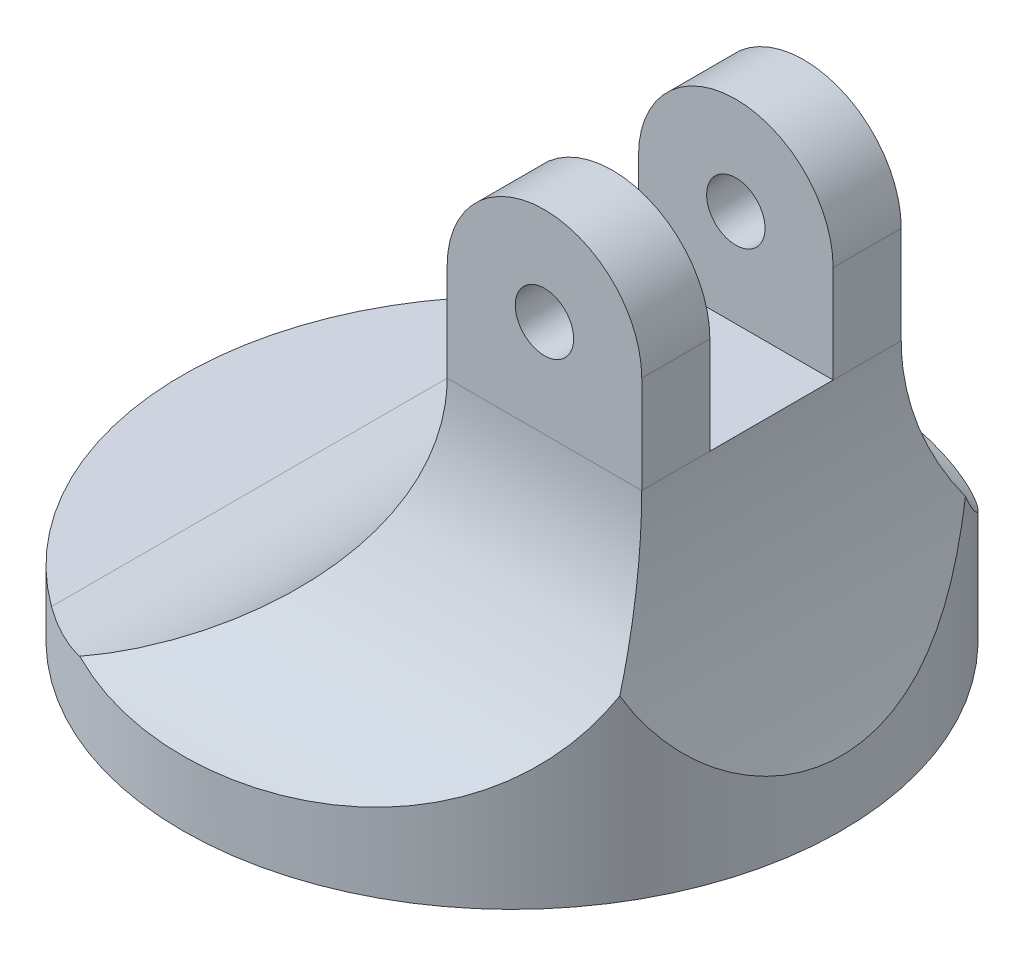
SolidWorks part; units mm, degrees
ref_plane "Front Plane" through (0, 0, 0) normal (0, 0, 1) x (1, 0, 0)
ref_plane "Top Plane" through (0, 0, 0) normal (0, 1, 0) x (1, 0, 0)
ref_plane "Right Plane" through (0, 0, 0) normal (1, 0, 0) x (0, 0, -1)
sketch "Sketch1" plane through (0, 0, 0) normal (0, 1, 0) x (1, 0, 0)
  circle A0 centre (0, 0) radius 25.4
  dimension "D1" = 50.8
extrude "base" add sketch "Sketch1" along normal blind 25
sketch "Sketch3" plane through (0, 0, 0) normal (0, 0, 1) x (1, 0, 0)
  line L0 (5, 25) -> (20, 25)
  line L1 (25.4, 25) -> (-25.4, 25) construction
  line L2 (-25.4, 5) -> (-15, 5)
  line L3 (-25.4, 25) -> (-25.4, 0) construction
  line L4 (-25.4, 0) -> (25.4, 0) construction
  line L5 (25.4, 0) -> (25.4, 25) construction
  line L6 (25.4, 5) -> (25.4, 0)
  line L7 (25.4, 0) -> (-25.4, 0)
  line L8 (-25.4, 0) -> (-25.4, 5)
  line L9 (0, 0) -> (0, 25) construction
  line L10 (20, 25) -> (20, 35) construction
  line L11 (5, 25) -> (5, 35) construction
  arc A0 (5, 25) -> (-15, 5) centre (-15, 25) cw
  arc A1 (20, 25) -> (25.4, 5) centre (59.737, 25) ccw
  point P5 (5, 35.7145)
  point P24 (15, 35.0456)
  point P25 (25.4, 7.1513)
  dimension "D1" = 15
  dimension "D2" = 5
  dimension "D3" = 5
  dimension "D4" = 10
extrude "Cut-Extrude1" cut sketch "Sketch3" against normal through all and the other way through all flip side to cut
sketch "Sketch4" plane through (0, 0, 0) normal (1, 0, 0) x (0, 0, -1)
  line L0 (-25.4, 5) -> (-25.4, 0)
  line L6 (-10, 25) -> (-10, 35.0758) construction
  line L7 (10, 25) -> (10, 35.0758) construction
  line L8 (-25.4, 0) -> (25.4, 0)
  line L9 (25.4, 0) -> (25.4, 5)
  line L10 (-25.4, 11.7714) -> (-25.4, 0) construction
  line L11 (25.4, 0) -> (25.4, 11.7713) construction
  line L14 (-10, 25) -> (10, 25)
  line L15 (-15.6576, 25) -> (15.6576, 25) construction
  arc A0 (-25.4, 5) -> (-10, 25) centre (-30.687, 25) ccw
  arc A1 (10, 25) -> (25.4, 5) centre (30.687, 25) ccw
  point P13 (0, 25)
  point P16 (-5, 35.5976)
  point P19 (35.4758, 4.6)
  point P21 (0, 0)
  point P22 (25.4, 25)
  point P23 (7.4956, 25)
  dimension "D1" = 5
  dimension "D2" = 20
extrude "Cut-Extrude2" cut sketch "Sketch4" against normal through all and the other way through all flip side to cut
sketch "Sketch5" plane through (0, 0, 0) normal (0, -1, 0) x (1, 0, 0)
  circle A0 centre (0, 0) radius 2.25
  dimension "D1" = 4.5
extrude "Cut-Extrude3" cut sketch "Sketch5" against normal through all
sketch "Sketch6" plane through (0, 25, 0) normal (0, 1, 0) x (1, 0, 0)
  circle A0 centre (0, 0) radius 4
  dimension "D1" = 8
extrude "Cut-Extrude4" cut sketch "Sketch6" against normal offset from surface (20 mm away) 5 up to face at (0, 0, -2.25)
sketch "Sketch7" plane through (0, 25, 0) normal (0, 1, 0) x (1, 0, 0)
  line L1 (5, 10) -> (20, 10)
  line L2 (5, 10) -> (5, -10)
  line L3 (5, -10) -> (20, -10)
  line L4 (20, 10) -> (20, -10)
extrude "arm base" add sketch "Sketch7" along normal blind 15
sketch "Sketch8" plane through (0, 0, -10) normal (0, 0, -1) x (-1, 0, 0)
  line L0 (-5, 40) -> (-5, 25) construction
  line L1 (-20, 40) -> (-20, 25) construction
  line L5 (-5, 32.5) -> (-5, 40)
  line L6 (-5, 40) -> (-20, 40)
  line L7 (-20, 40) -> (-20, 32.5)
  arc A0 (-5, 32.5) -> (-20, 32.5) centre (-12.5, 32.5) ccw
  circle A1 centre (-12.5, 32.5) radius 2.25
  line M6 (-5, 25) -> (-5, 40)
  line M7 (-5, 40) -> (-20, 40)
  line M8 (-20, 40) -> (-20, 25)
  dimension "D1" = 4.5
extrude "arm hole" cut sketch "Sketch8" against normal through all contours A0 M6 M7 | A0 L6 M8 | A1
sketch "Sketch9" plane through (20, 0, 0) normal (1, 0, 0) x (0, 0, -1)
  line L0 (-10, 25) -> (10, 25) construction
  line L1 (4.75, 25) -> (-4.75, 25)
  line L2 (4.75, 25) -> (4.75, 40)
  line L3 (4.75, 40) -> (-4.75, 40)
  line L4 (-4.75, 25) -> (-4.75, 40)
  line L5 (10, 40) -> (-10, 40) construction
  point P8 (-6.4721, 25)
  point P9 (0, 25)
  dimension "D1" = 9.5
extrude "Cut-Extrude7" cut sketch "Sketch9" against normal through all
